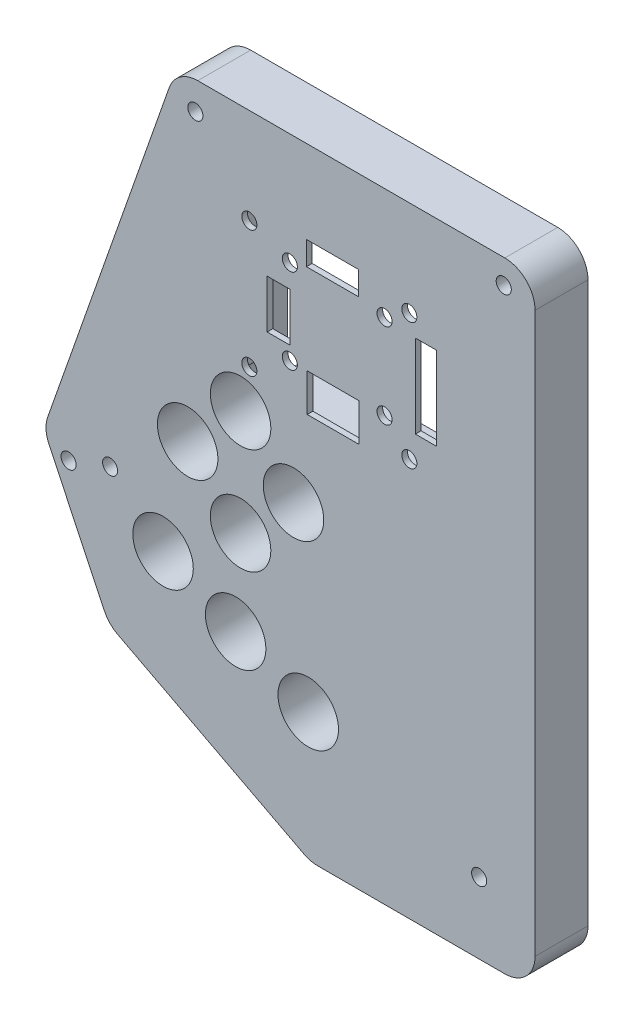
SolidWorks part; units mm, degrees
ref_plane "Front Plane" through (0, 0, 0) normal (0, 0, 1) x (1, 0, 0)
ref_plane "Top Plane" through (0, 0, 0) normal (0, 1, 0) x (1, 0, 0)
ref_plane "Right Plane" through (0, 0, 0) normal (1, 0, 0) x (0, 0, -1)
sketch "Sketch1" plane through (0, 0, 0) normal (0, 0, 1) x (1, 0, 0)
  line L6 (-20.066, -57.15) -> (46.99, -57.15) construction
  line L7 (-12.446, -73.152) -> (46.99, -73.152) construction
  line L8 (-3.3141, 6.35) -> (48.26, 6.35)
  line L9 (53.34, 1.27) -> (53.34, -92.71)
  line L10 (48.26, -97.79) -> (16.847, -97.79)
  line L16 (-8.1072, 2.9529) -> (-28.5162, -55.1739)
  line L18 (-20.066, -57.15) -> (-29.21, -57.15) construction
  line L26 (0, 0) -> (46.99, 0) construction
  line L27 (46.99, 0) -> (46.99, -88.9) construction
  line L28 (46.99, -88.9) -> (17.78, -88.9) construction
  line L29 (17.78, -88.9) -> (-12.446, -73.152) construction
  line L30 (-12.446, -73.152) -> (-20.066, -57.15) construction
  line L31 (-20.066, -57.15) -> (0, 0) construction
  line L32 (46.99, -57.15) -> (46.99, -88.9) construction
  line L33 (17.78, -88.9) -> (15.603, -97.79) construction
  line L34 (-12.446, -73.152) -> (-17.9301, -78.4424) construction
  line L35 (14.4997, -97.2152) -> (-16.7505, -80.9336)
  line L36 (-28.3096, -59.0409) -> (-18.9898, -78.6124)
  arc A0 (53.34, -92.71) -> (48.26, -97.79) centre (48.26, -92.71) cw
  arc A1 (48.26, 6.35) -> (53.34, 1.27) centre (48.26, 1.27) cw
  arc A2 (-8.1072, 2.9529) -> (-3.3141, 6.35) centre (-3.3141, 1.27) cw
  arc A3 (14.4997, -97.2152) -> (16.847, -97.79) centre (16.847, -92.71) ccw
  arc A4 (-16.7505, -80.9336) -> (-18.9898, -78.6124) centre (-14.4033, -76.4284) cw
  arc A5 (-28.5162, -55.1739) -> (-28.3096, -59.0409) centre (-23.723, -56.8568) ccw
  point P16 (53.34, -97.79)
  point P20 (53.34, 6.35)
  dimension "D8" = 5.08
  dimension "D9" = 5.08
  dimension "D1" = 88.9
  dimension "D2" = 29.21
  dimension "D3" = 59.436
  dimension "D4" = 67.056
  dimension "D5" = 104.14
  dimension "D6" = 82.55
  dimension "D7" = 46.99
  dimension "D13" = 103.76
  dimension "D17" = 108.51
extrude "Boss-Extrude1" add sketch "Sketch1" along normal blind 8.89
sketch "Sketch3" plane through (0, 0, 8.89) normal (0, 0, 1) x (1, 0, 0)
  line L6 (-20.066, -57.15) -> (46.99, -57.15) construction
  line L7 (-12.446, -73.152) -> (46.99, -73.152) construction
  line L8 (0, 0) -> (46.99, 0) construction
  line L9 (46.99, 0) -> (46.99, -88.9) construction
  line L10 (46.99, -88.9) -> (17.78, -88.9) construction
  line L11 (17.78, -88.9) -> (-12.446, -73.152) construction
  line L12 (-12.446, -73.152) -> (-20.066, -57.15) construction
  line L13 (-20.066, -57.15) -> (0, 0) construction
  line L14 (3.8784, -55.88) -> (3.8784, -38.1) construction
  circle A0 centre (3.8784, -38.1) radius 5.08
  circle A1 centre (-5.0116, -46.99) radius 5.08
  circle A2 centre (3.8784, -55.88) radius 5.08
  circle A3 centre (12.7684, -46.99) radius 5.08
  circle A4 centre (-9.144, -65.024) radius 5.08
  circle A5 centre (3.048, -70.612) radius 5.08
  circle A6 centre (15.24, -76.2) radius 5.08
  dimension "D7" = 10.16
  dimension "D1" = 43.1116
  dimension "D2" = 8.89
  dimension "D3" = 8.89
  dimension "D4" = 46.99
  dimension "D5" = 8.89
  dimension "D6" = 8.89
  dimension "D8" = 12.192
  dimension "D9" = 5.588
  dimension "D10" = 5.588
  dimension "D11" = 12.192
  dimension "D12" = 43.942
  dimension "D13" = 70.612
sketch "Sketch4" plane through (0, 0, 0) normal (0, 0, 1) x (1, 0, 0)
  line L0 (2.8795, -3.175) -> (2.8795, -33.655)
  line L6 (2.8795, -3.175) -> (37.1695, -3.175)
  line L9 (37.1695, -3.175) -> (37.1695, -33.655)
  line L48 (37.1695, -33.655) -> (2.8795, -33.655)
  line L50 (46.99, 0) -> (46.99, -88.9) construction
  dimension "D1" = 9.8205
  dimension "D2" = 34.29
  dimension "D3" = 30.48
sketch "Sketch9" plane through (0, 0, 0) normal (0, 0, -1) x (-1, 0, 0)
  line L0 (-46.99, 0) -> (-46.99, -88.9) construction
  line L7 (-36.7885, -35.5217) -> (-36.7885, -40.4326) construction
  line L8 (-53.34, -92.71) -> (-53.34, 1.27) construction
  line L9 (-48.26, 6.35) -> (3.3141, 6.35) construction
  line L25 (-3.2605, -20.3148) -> (-36.7885, -20.3148) construction
  line L26 (-33.4865, -32.221) -> (-29.908, -32.221) construction
  line L27 (-33.4865, -33.0148) -> (-33.4865, -29.5416) construction
  line L28 (-4.0809, -8.4085) -> (-4.0809, -11.8133) construction
  line L29 (-4.0809, -8.4085) -> (-9.1758, -8.4085) construction
  line L30 (-5.0385, -17.1398) -> (-5.005, -17.1398) construction
  line L31 (-5.0385, -7.6148) -> (-5.0652, -7.6148) construction
  line L32 (-8.3409, -24.3788) -> (-8.3409, -16.2508)
  line L33 (-15.0648, -33.0148) -> (-23.8027, -33.0148)
  line L34 (-36.7885, -26.7831) -> (-33.2325, -26.7831)
  line L35 (-36.7885, -12.8131) -> (-36.7885, -26.7831)
  line L36 (-14.9445, -7.6148) -> (-23.6757, -7.6148)
  line L37 (-23.6757, -7.6148) -> (-23.6757, -11.5835)
  line L38 (-15.0648, -33.0148) -> (-15.0648, -26.6648)
  line L39 (-23.8027, -26.6648) -> (-23.8027, -33.0148)
  line L40 (-12.1509, -24.3788) -> (-8.3409, -24.3788)
  line L41 (-8.3409, -16.2508) -> (-12.1509, -16.2508)
  line L42 (-33.2325, -12.8131) -> (-36.7885, -12.8131)
  line L43 (-12.1509, -16.2508) -> (-12.1509, -24.3788)
  line L44 (-14.9445, -11.5835) -> (-23.6757, -11.5835)
  line L45 (-14.9445, -7.6148) -> (-14.9445, -11.5835)
  line L46 (-23.8027, -26.6648) -> (-20.9135, -26.6648)
  line L47 (-15.0648, -26.6648) -> (-20.9135, -26.6648)
  line L48 (-33.2325, -12.8131) -> (-33.2325, -26.7831)
  circle A8 centre (-5.3484, -30.9535) radius 1.2675
  circle A9 centre (-32.219, -9.6761) radius 1.2675
  circle A10 centre (-12.1505, -12.3773) radius 1.2675
  circle A11 centre (-12.1505, -26.6648) radius 1.2675
  circle A12 centre (-28.0572, -12.3773) radius 1.2675
  circle A13 centre (-5.3484, -9.6761) radius 1.2675
  circle A14 centre (-32.219, -30.9535) radius 1.2675
  circle A15 centre (-28.0572, -26.6648) radius 1.2675
  dimension "D1" = 2.535
  dimension "D2" = 10.2015
  dimension "D3" = 16.5515
  dimension "D4" = 19.1631
  dimension "D5" = 13.97
extrude "Cut-Extrude6" cut sketch "Sketch9" against normal through all both and the other way through all
extrude "Cut-Extrude7" cut sketch "Sketch4" along normal blind 7.9375 and the other way through all
extrude "Cut-Extrude8" cut sketch "Sketch3" against normal through all both and the other way through all
sketch "Sketch12" plane through (0, 0, 0) normal (0, 0, -1) x (-1, 0, 0)
  line L0 (-48.26, 6.35) -> (3.3141, 6.35) construction
  line L1 (-53.34, -92.71) -> (-53.34, 1.27) construction
  line L2 (8.1072, 2.9529) -> (28.5162, -55.1739) construction
  line L3 (28.3096, -59.0409) -> (18.9898, -78.6124) construction
  circle A0 centre (-48.0822, 2.286) radius 1.27
  circle A1 centre (3.7187, 1.651) radius 1.27
  circle A2 centre (25.0123, -59.762) radius 1.27
  dimension "D1" = 2.54
  dimension "D2" = 4.064
  dimension "D3" = 5.2578
  dimension "D4" = 4.699
  dimension "D5" = 4.572
  dimension "D6" = 4.826
  dimension "D7" = 2.667
extrude "Cut-Extrude9" cut sketch "Sketch12" against normal through all both and the other way through all
sketch "Sketch15" plane through (0, 0, 0) normal (0, 0, -1) x (-1, 0, 0)
  line L0 (-37.465, -31.4407) -> (-43.942, -85.852) construction
  line L1 (20.066, -57.15) -> (18.034, -57.15) construction
  line L2 (20.066, -57.15) -> (-46.99, -57.15) construction
  circle A0 centre (18.034, -57.15) radius 1.27
  circle A1 centre (-43.942, -85.852) radius 1.27
  dimension "D1" = 2.54
  dimension "D2" = 2.032
  dimension "D3" = 54.7954
extrude "Cut-Extrude10" cut sketch "Sketch15" against normal through all both and the other way through all
